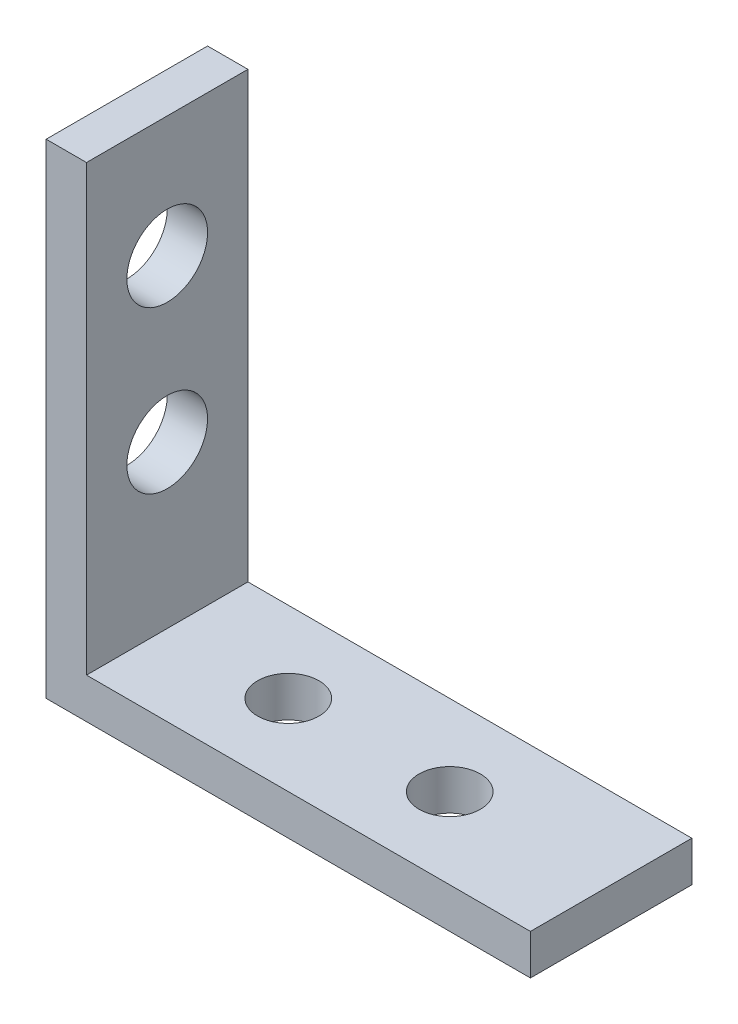
SolidWorks part; units mm, degrees
ref_plane "Front Plane" through (0, 0, 0) normal (0, 0, 1) x (1, 0, 0)
ref_plane "Top Plane" through (0, 0, 0) normal (0, 1, 0) x (1, 0, 0)
ref_plane "Right Plane" through (0, 0, 0) normal (1, 0, 0) x (0, 0, -1)
sketch "Sketch1" plane through (0, 0, 0) normal (0, 0, 1) x (1, 0, 0)
  line L0 (0, 0) -> (0, 38.1)
  line L1 (0, 38.1) -> (3.175, 38.1)
  line L2 (3.175, 38.1) -> (3.175, 3.175)
  line L3 (3.175, 3.175) -> (38.1, 3.175)
  line L4 (38.1, 3.175) -> (38.1, 0)
  line L5 (38.1, 0) -> (0, 0)
  dimension "D1" = 3.175
  dimension "D2" = 3.175
  dimension "D3" = 38.1
  dimension "D4" = 38.1
extrude "Boss-Extrude1" add sketch "Sketch1" along normal blind 12.7
sketch "Sketch2" plane through (0, 3.175, 0) normal (0, 1, 0) x (1, 0, 0)
  line L0 (38.1, -6.35) -> (3.175, -6.35) construction
  line L1 (38.1, -12.7) -> (38.1, 0) construction
  line L2 (3.175, -12.7) -> (3.175, 0) construction
  line L3 (0, -12.7) -> (0, 0) construction
  circle A0 centre (12.7, -6.35) radius 2.413
  circle A1 centre (25.4, -6.35) radius 2.413
  dimension "D1" = 4.826
  dimension "D3" = 12.7
  dimension "D2" = 12.7
extrude "Cut-Extrude1" cut sketch "Sketch2" against normal through all
sketch "Sketch3" plane through (3.175, 0, 0) normal (1, 0, 0) x (0, 0, -1)
  line L0 (-6.35, 38.1) -> (-6.35, 3.175) construction
  line L1 (-12.7, 38.1) -> (0, 38.1) construction
  line L2 (-12.7, 3.175) -> (0, 3.175) construction
  line L3 (-12.7, 0) -> (0, 0) construction
  circle A0 centre (-6.35, 28.575) radius 3.175
  circle A1 centre (-6.35, 15.875) radius 3.175
  dimension "D1" = 6.35
  dimension "D2" = 12.7
  dimension "D3" = 15.875
extrude "Cut-Extrude2" cut sketch "Sketch3" against normal through all
